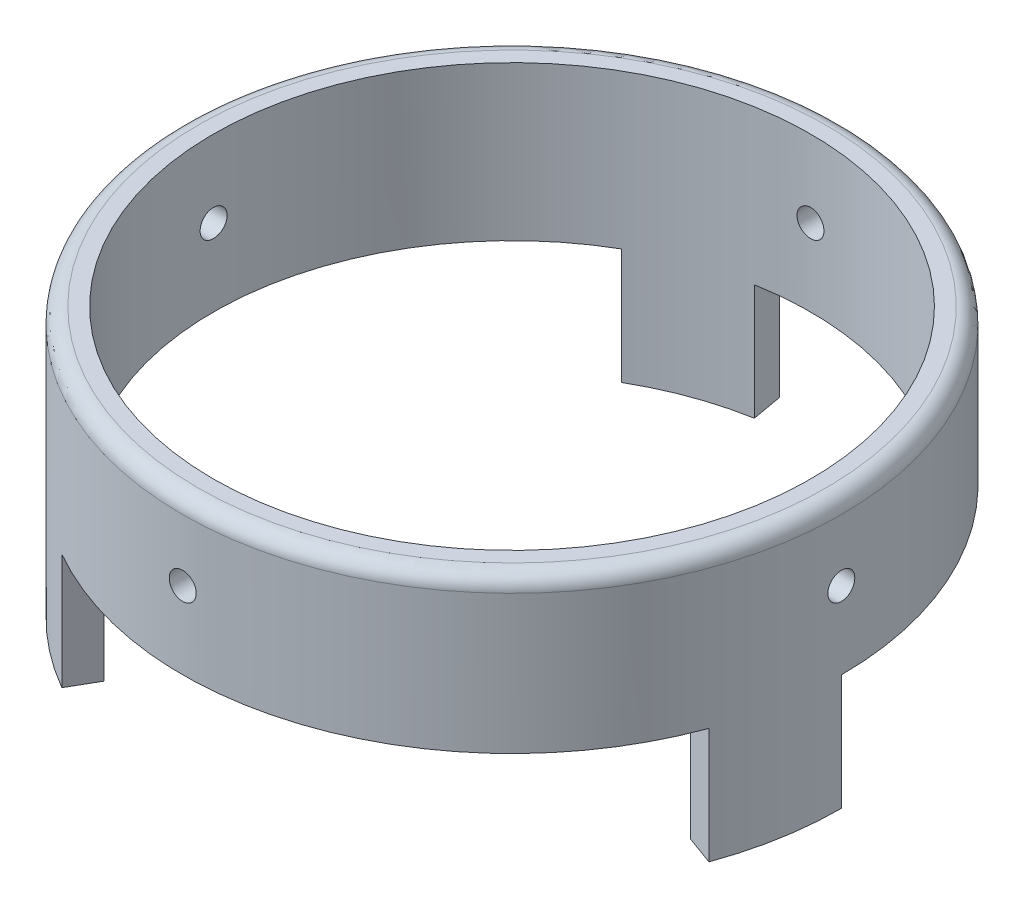
SolidWorks part; units mm, degrees
ref_plane "Front Plane" through (0, 0, 0) normal (0, 0, 1) x (1, 0, 0)
ref_plane "Top Plane" through (0, 0, 0) normal (0, 1, 0) x (1, 0, 0)
ref_plane "Right Plane" through (0, 0, 0) normal (1, 0, 0) x (0, 0, -1)
sketch "Sketch1" plane through (0, 0, 0) normal (0, 1, 0) x (1, 0, 0)
  circle A0 centre (0, 0) radius 38.75
  circle A1 centre (0, 0) radius 42.75
  dimension "D1" = 77.5
  dimension "D2" = 4
extrude "Boss-Extrude1" add sketch "Sketch1" along normal blind 20
sketch "Sketch2" plane through (0, 0, 0) normal (0, -1, 0) x (1, 0, 0)
  line L0 (0, 0) -> (40.1719, 14.6214) construction
  line L1 (0, 0) -> (42.75, 0) construction
  line L2 (40.1719, 14.6214) -> (36.4131, 13.2533)
  line L3 (38.75, 0) -> (42.75, 0)
  line L4 (-7.4235, -42.1005) -> (-6.7289, -38.1613)
  line L5 (-19.375, -33.5585) -> (-21.375, -37.0226)
  line L6 (-32.7484, 27.4792) -> (-29.6842, 24.908)
  line L7 (-19.375, 33.5585) -> (-21.375, 37.0226)
  circle A0 centre (0, 0) radius 42.75 construction
  circle A1 centre (0, 0) radius 38.75 construction
  arc A2 (38.75, 0) -> (36.4131, 13.2533) centre (0, 0) ccw
  arc A3 (42.75, 0) -> (40.1719, 14.6214) centre (0, 0) ccw
  arc A4 (-21.375, -37.0226) -> (-7.4235, -42.1005) centre (0, 0) ccw
  arc A5 (-19.375, -33.5585) -> (-6.7289, -38.1613) centre (0, 0) ccw
  arc A6 (-21.375, 37.0226) -> (-32.7484, 27.4792) centre (0, 0) ccw
  arc A7 (-19.375, 33.5585) -> (-29.6842, 24.908) centre (0, 0) ccw
  point P24 (0, 0)
  dimension "D1" = 20
  dimension "D2" = 3
extrude "Boss-Extrude2" add sketch "Sketch2" along normal blind 15
sketch "Sketch3" plane through (0, 0, 0) normal (0, 0, 1) x (1, 0, 0)
  line L0 (0, 0) -> (0, 10) construction
  line L1 (42.75, 20) -> (-42.75, 20) construction
  circle A0 centre (0, 10) radius 1.75
  dimension "D2" = 3.5
  dimension "D1" = 10
extrude "Cut-Extrude1" cut sketch "Sketch3" against normal through all both and the other way through all
sketch "Sketch4" plane through (0, 0, 0) normal (1, 0, 0) x (0, 0, -1)
  line L0 (0, 0) -> (0, 10) construction
  line L1 (42.75, 20) -> (-42.75, 20) construction
  circle A0 centre (0, 10) radius 1.75
  dimension "D1" = 3.5
  dimension "D2" = 10
extrude "Cut-Extrude2" cut sketch "Sketch4" against normal through all both and the other way through all
fillet "Fillet1" radius 2 1 edges at (0, 20, 42.75)
